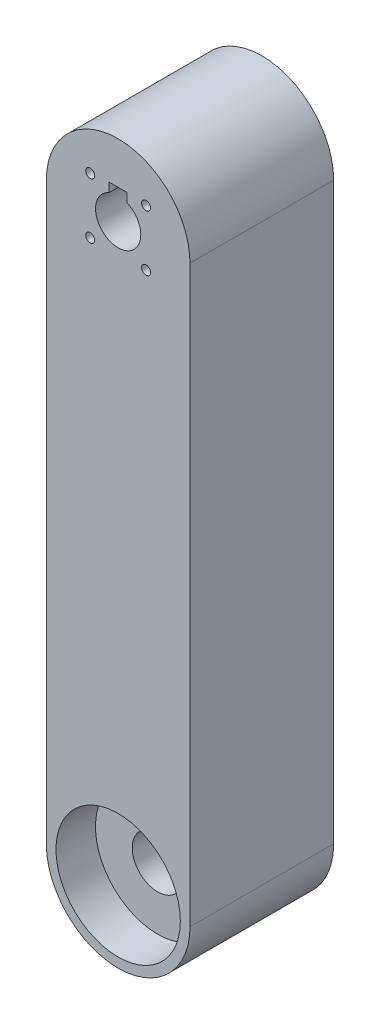
SolidWorks part; units mm, degrees
ref_plane "Front Plane" through (0, 0, 0) normal (0, 0, 1) x (1, 0, 0)
ref_plane "Top Plane" through (0, 0, 0) normal (0, 1, 0) x (1, 0, 0)
ref_plane "Right Plane" through (0, 0, 0) normal (1, 0, 0) x (0, 0, -1)
sketch "Sketch1" plane through (0, 0, 0) normal (0, 0, 1) x (1, 0, 0)
  line L2 (12.7, 50.8) -> (12.7, -50.8)
  line L4 (-12.7, 50.8) -> (-12.7, -50.8)
  line L5 (12.7, 50.8) -> (-12.7, -50.8) construction
  line L6 (12.7, -50.8) -> (-12.7, 50.8) construction
  arc A0 (-12.7, 50.8) -> (12.7, 50.8) centre (0, 50.8) cw
  arc A1 (-12.7, -50.8) -> (12.7, -50.8) centre (0, -50.8) ccw
  point P0 (0, 0)
  dimension "D1" = 101.6
  dimension "D2" = 25.4
extrude "Boss-Extrude1" add sketch "Sketch1" along normal blind 25.4
sketch "Sketch2" plane through (0, 0, 25.4) normal (0, 0, 1) x (1, 0, 0)
  line L0 (-4.9391, 55.7391) -> (4.9391, 45.8609) construction
  line L1 (4.9391, 55.7391) -> (-4.9391, 45.8609) construction
  line L2 (0, 50.8) -> (0, 59.0413) construction
  circle A0 centre (0, 50.8) radius 4
  circle A1 centre (-4.9391, 55.7391) radius 0.7938
  circle A2 centre (-4.9391, 45.8609) radius 0.7937
  circle A3 centre (4.9391, 55.7391) radius 0.7938
  circle A4 centre (4.9391, 45.8609) radius 0.7938
  point P8 (0, 50.8)
  point P9 (0, 50.8)
  dimension "D1" = 8
  dimension "D4" = 1.5875
  dimension "D2" = 45
  dimension "D3" = 13.97
extrude "Cut-Extrude1" cut sketch "Sketch2" against normal up to next
sketch "Sketch3" plane through (0, 0, 25.4) normal (0, 0, 1) x (1, 0, 0)
  line L1 (-1.5875, 56.059) -> (1.5875, 56.059)
  line L2 (-1.5875, 56.059) -> (-1.5875, 54.4715)
  line L3 (-1.5875, 54.4715) -> (1.5875, 54.4715)
  line L4 (1.5875, 56.059) -> (1.5875, 54.4715)
  circle A0 centre (0, 50.8) radius 4 construction
  dimension "D1" = 3.175
  dimension "D2" = 1.5875
extrude "Cut-Extrude2" cut sketch "Sketch3" against normal through all
sketch "Sketch4" plane through (0, 0, 25.4) normal (0, 0, 1) x (1, 0, 0)
  circle A0 centre (0, -50.8) radius 10.9919
  dimension "D1" = 21.9837
extrude "Cut-Extrude3" cut sketch "Sketch4" against normal blind 6.985
ref_plane "Plane1" through (0, 0, 12.7) normal (0, 0, 1) x (1, 0, 0)
mirror "Mirror1" about plane through (0, 0, 12.7) normal (0, 0, 1) of "Cut-Extrude3"
sketch "Sketch5" plane through (0, 0, 18.415) normal (0, 0, 1) x (1, 0, 0)
  circle A0 centre (0, -50.8) radius 4.5
  circle A1 centre (0, -50.8) radius 10.9919 construction
  dimension "D1" = 9
extrude "Cut-Extrude4" cut sketch "Sketch5" against normal through all
